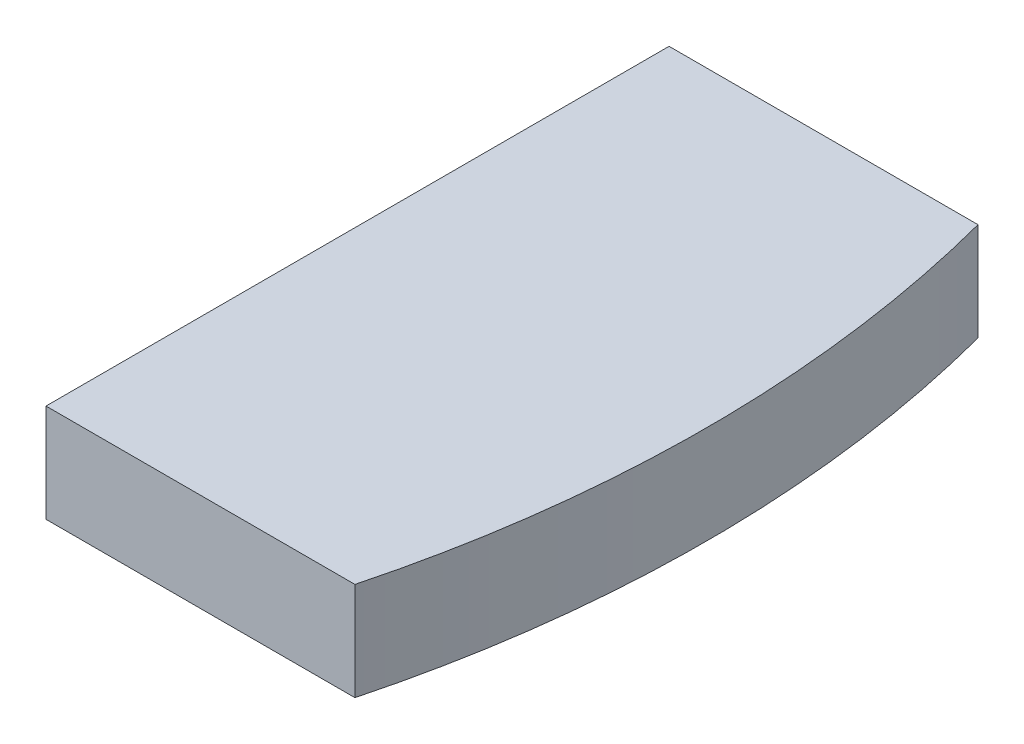
SolidWorks part; units mm, degrees
ref_plane "Front Plane" through (0, 0, 0) normal (0, 0, 1) x (1, 0, 0)
ref_plane "Top Plane" through (0, 0, 0) normal (0, 1, 0) x (1, 0, 0)
ref_plane "Right Plane" through (0, 0, 0) normal (1, 0, 0) x (0, 0, -1)
sketch "Sketch1" plane through (0, 0, 0) normal (0, 1, 0) x (1, 0, 0)
  line L0 (67.2724, 38.8397) -> (129.9038, 75)
  line L1 (0, 0) -> (150, 0) construction
  line L2 (67.2724, -38.8397) -> (129.9038, -75)
  line L4 (62.2724, 37.5) -> (-45.0481, 37.5)
  line L5 (62.2724, -37.5) -> (-45.0481, -37.5)
  line L6 (-55.0481, 27.5) -> (-55.0481, -27.5)
  arc A0 (129.9038, -75) -> (129.9038, 75) centre (0, 0) ccw
  circle A1 centre (0, 0) radius 15
  circle A2 centre (30, 0) radius 5
  circle A3 centre (-30, 0) radius 5
  circle A4 centre (50, 0) radius 5
  arc A5 (67.2724, 38.8397) -> (62.2724, 37.5) centre (62.2724, 47.5) cw
  arc A6 (67.2724, -38.8397) -> (62.2724, -37.5) centre (62.2724, -47.5) ccw
  arc A7 (-55.0481, -27.5) -> (-45.0481, -37.5) centre (-45.0481, -27.5) ccw
  arc A8 (-45.0481, 37.5) -> (-55.0481, 27.5) centre (-45.0481, 27.5) ccw
  point P19 (64.9519, 37.5)
  point P22 (64.9519, -37.5)
  point P25 (-55.0481, -37.5)
  point P28 (-55.0481, 37.5)
  dimension "D1" = 300
  dimension "D6" = 30
  dimension "D7" = 10
  dimension "D9" = 10
  dimension "D11" = 10
  dimension "D13" = 10
  dimension "D2" = 30
  dimension "D3" = 120
  dimension "D4" = 75
  dimension "D5" = 75
  dimension "D8" = 30
  dimension "D10" = 30
  dimension "D12" = 20
extrude "Boss-Extrude1" add sketch "Sketch1" along normal blind 12
sketch "Sketch3" plane through (0, 12, 0) normal (0, 1, 0) x (1, 0, 0)
  line L0 (0, 0) -> (150, 0) construction
  line L1 (107.3, 38.1) -> (107.3, -38.1)
  line L2 (107.3, 38.1) -> (132.7, 38.1) construction
  line L3 (107.3, 38.1) -> (107.3, -38.1) construction
  line L4 (107.3, -38.1) -> (132.7, -38.1) construction
  line L5 (132.7, 38.1) -> (132.7, -38.1) construction
  line L6 (107.3, 38.1) -> (132.7, -38.1) construction
  line L7 (107.3, -38.1) -> (132.7, 38.1) construction
  line L8 (107.3, 38.1) -> (155.3028, 38.1)
  line L9 (107.3, -38.1) -> (155.3028, -38.1)
  line L10 (155.3028, 38.1) -> (155.3028, -38.1)
  arc A0 (129.9038, -75) -> (129.9038, 75) centre (0, 0) ccw construction
  point P6 (120, 0)
  circle M9 centre (-30, 0) radius 5
  circle M10 centre (0, 0) radius 15
  arc M11 (129.9038, -75) -> (129.9038, 75) centre (0, 0) ccw
  line M12 (129.9038, 75) -> (67.2724, 38.8397)
  arc M13 (67.2724, 38.8397) -> (62.2724, 37.5) centre (62.2724, 47.5) cw
  line M14 (62.2724, 37.5) -> (-45.0481, 37.5)
  arc M15 (-45.0481, 37.5) -> (-55.0481, 27.5) centre (-45.0481, 27.5) ccw
  line M16 (-55.0481, 27.5) -> (-55.0481, -27.5)
  arc M17 (-55.0481, -27.5) -> (-45.0481, -37.5) centre (-45.0481, -27.5) ccw
  line M18 (-45.0481, -37.5) -> (62.2724, -37.5)
  arc M19 (62.2724, -37.5) -> (67.2724, -38.8397) centre (62.2724, -47.5) cw
  line M20 (67.2724, -38.8397) -> (129.9038, -75)
  circle M21 centre (30, 0) radius 5
  circle M22 centre (50, 0) radius 5
  dimension "D1" = 25.4
  dimension "D2" = 76.2
  dimension "D3" = 120
extrude "Cut-Extrude4" cut sketch "Sketch3" against normal through all contours L9 L1 L8 M11 M12 M13 M14 M15 M16 M17 M18 M19 M20 M10 M21 M22 M9
